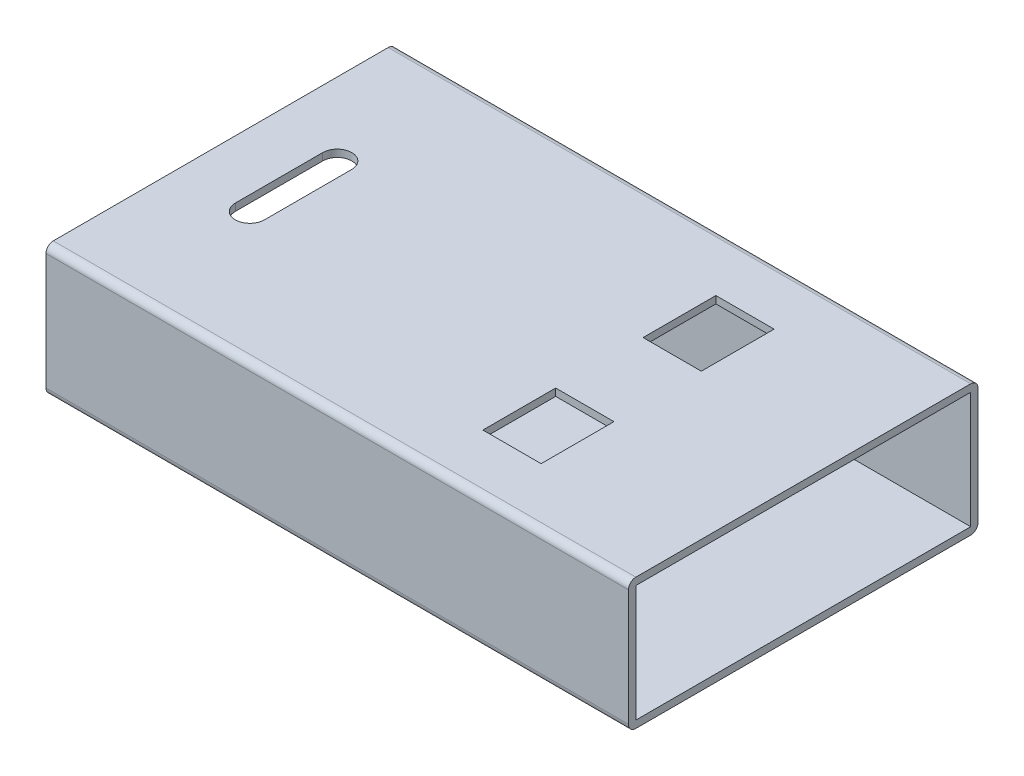
SolidWorks part; units mm, degrees
ref_plane "Front Plane" through (0, 0, 0) normal (0, 0, 1) x (1, 0, 0)
ref_plane "Top Plane" through (0, 0, 0) normal (0, 1, 0) x (1, 0, 0)
ref_plane "Right Plane" through (0, 0, 0) normal (1, 0, 0) x (0, 0, -1)
other "Configuration Table"
sketch "Main_shell_sketch" plane through (0, 0, 0) normal (1, 0, 0) x (0, 0, -1)
  line L1 (-5.75, -2.25) -> (5.75, -2.25)
  line L2 (-6, -2) -> (-6, 2)
  line L3 (-5.75, 2.25) -> (5.75, 2.25)
  line L4 (6, -2) -> (6, 2)
  line L5 (-6, -2.25) -> (6, 2.25) construction
  line L6 (-6, 2.25) -> (6, -2.25) construction
  arc A0 (5.75, 2.25) -> (6, 2) centre (5.75, 2) cw
  arc A1 (5.75, -2.25) -> (6, -2) centre (5.75, -2) ccw
  arc A2 (-5.75, -2.25) -> (-6, -2) centre (-5.75, -2) cw
  arc A3 (-6, 2) -> (-5.75, 2.25) centre (-5.75, 2) cw
  point P0 (0, 0)
  dimension "D3" = 0.25
  dimension "D1" = 12
  dimension "D2" = 4.5
extrude "Main_shell" add sketch "Main_shell_sketch" against normal blind 20 thin
sketch "Connector_hole_sketch" plane through (0, 2.25, 0) normal (0, 1, 0) x (1, 0, 0)
  line L0 (-20, 0) -> (0, 0) construction
  line L1 (-20, 5.75) -> (-20, -5.75) construction
  line L2 (0, 5.75) -> (0, -5.75) construction
  line L3 (-7, 1.5) -> (-7, 4)
  line L4 (-7, -1.5) -> (-5, -1.5)
  line L5 (-7, -1.5) -> (-7, -4)
  line L6 (-7, -4) -> (-5, -4)
  line L7 (-5, -1.5) -> (-5, -4)
  line L8 (-7, -1.5) -> (-5, -4) construction
  line L9 (-7, -4) -> (-5, -1.5) construction
  line L10 (-7, 1.5) -> (-5, 4) construction
  line L11 (-7, 4) -> (-5, 1.5) construction
  line L12 (-7, 1.5) -> (-5, 1.5)
  line L13 (-5, 1.5) -> (-5, 4)
  line L14 (-7, 4) -> (-5, 4)
  line L15 (-20, -6) -> (0, -6) construction
  line L16 (-17.5, -1.5) -> (-17.5, 1.5) construction
  line L17 (-18, -1.5) -> (-18, 1.5)
  line L18 (-17, -1.5) -> (-17, 1.5)
  arc A0 (-18, -1.5) -> (-17, -1.5) centre (-17.5, -1.5) ccw
  arc A1 (-17, 1.5) -> (-18, 1.5) centre (-17.5, 1.5) ccw
  point P6 (-6, -2.75)
  point P15 (-6, 2.75)
  point P20 (-17.5, 0)
  dimension "D6" = 0.5
  dimension "D1" = 2.5
  dimension "D2" = 2
  dimension "D3" = 2
  dimension "D4" = 5
  dimension "D5" = 3
  dimension "D7" = 2
extrude "Connector_holes" cut sketch "Connector_hole_sketch" against normal through all
